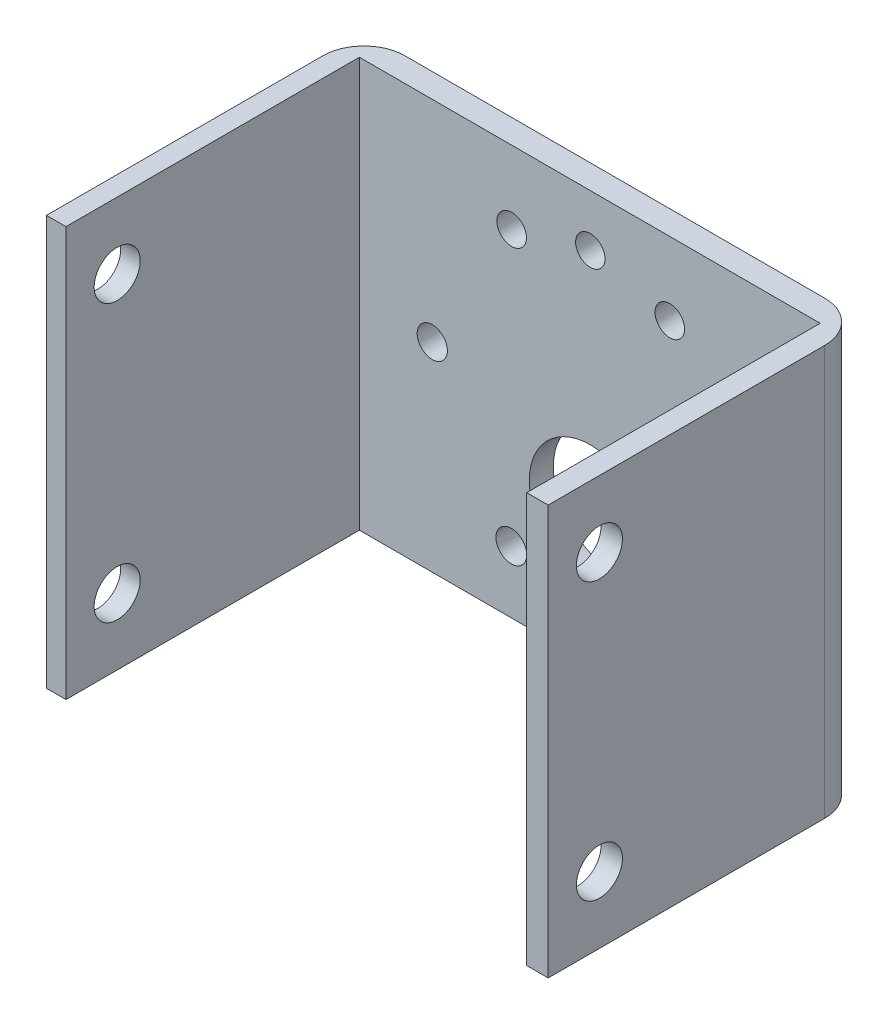
SolidWorks part; units mm, degrees
material "AISI 304"
ref_plane "Front Plane" through (0, 0, 0) normal (0, 0, 1) x (1, 0, 0)
ref_plane "Top Plane" through (0, 0, 0) normal (0, 1, 0) x (1, 0, 0)
ref_plane "Right Plane" through (0, 0, 0) normal (1, 0, 0) x (0, 0, -1)
sketch "Sketch1" plane through (0, 0, 0) normal (0, 1, 0) x (1, 0, 0)
  line L0 (-22.4033, -15.5) -> (-22.4033, 13.1532)
  line L1 (-24.5, 15.5) -> (24.5, 15.5)
  line L2 (-24.5, 15.5) -> (-24.5, -15.5)
  line L3 (-24.5, -15.5) -> (-22.4033, -15.5)
  line L4 (24.5, 15.5) -> (24.5, -15.5)
  line L7 (-22.4033, 13.1532) -> (22.2142, 13.1532)
  line L8 (22.2142, 13.1532) -> (22.2142, -15.5)
  line L10 (22.2142, -15.5) -> (24.5, -15.5)
  point P0 (0, 0)
  dimension "D1" = 31
  dimension "D2" = 49
extrude "Boss-Extrude1" add sketch "Sketch1" along normal blind 40
fillet "Fillet1" radius 4 2 edges at (24.5, 20, -15.5) (-24.5, 20, -15.5)
sketch "Sketch2" plane through (0, 0, -15.5) normal (0, 0, -1) x (-1, 0, 0)
  circle A0 centre (14, 20) radius 1.5
  circle A9 centre (-17, 20) radius 1.5
  circle A10 centre (-1.5, 4.5) radius 1.5
  circle A11 centre (-1.5, 35.5) radius 1.5
  circle A12 centre (-9.25, 6.5766) radius 1.5
  circle A13 centre (-9.25, 33.4234) radius 1.5
  circle A14 centre (6.25, 33.4234) radius 1.5
  circle A15 centre (6.25, 6.5766) radius 1.5
  circle A16 centre (-1.5, 13) radius 6
extrude "Cut-Extrude1" cut sketch "Sketch2" against normal blind 40
sketch "Sketch3" plane through (-24.5, 0, 0) normal (-1, 0, 0) x (0, 0, 1)
  line L0 (15.5, 40) -> (15.5, 0) construction
  line L1 (-11.5, 0) -> (15.5, 0) construction
  line L2 (-11.5, 40) -> (15.5, 40) construction
  circle A0 centre (10.5, 6.5) radius 2.25
  circle A1 centre (10.5, 33.5) radius 2.25
  dimension "D1" = 5
  dimension "D2" = 5
  dimension "D3" = 6.5
  dimension "D4" = 6.5
extrude "Cut-Extrude2" cut sketch "Sketch3" against normal blind 76
sketch "Sketch4" plane through (0, 0, -15.5) normal (0, 0, -1) x (-1, 0, 0)
  circle A0 centre (6.25, 33.4234) radius 1.5
  circle A1 centre (14, 20) radius 1.5
  circle A2 centre (6.25, 6.5766) radius 1.5
  circle A3 centre (-1.5, 4.5) radius 1.5
  circle A4 centre (-9.25, 6.5766) radius 1.5
  circle A5 centre (-17, 20) radius 1.5
  circle A6 centre (-1.5, 35.5) radius 1.5
  circle A7 centre (-9.25, 33.4234) radius 1.5
  circle A8 centre (-1.5, 13) radius 6
extrude "Boss-Extrude2" add sketch "Sketch4" against normal up to surface (2.3468 mm away) up to face at (-15.5, 20, -13.1532)
sketch "Sketch5" plane through (0, 0, -15.5) normal (0, 0, -1) x (-1, 0, 0)
  circle A1 centre (15.5, 20) radius 1.5
  circle A2 centre (0, 4.5) radius 1.5
  circle A3 centre (-15.5, 20) radius 1.5
  circle A4 centre (0, 35.5) radius 1.5
  circle A5 centre (7.75, 33.4234) radius 1.5
  circle A6 centre (-7.75, 33.4234) radius 1.5
  circle A7 centre (-7.75, 6.5766) radius 1.5
  circle A8 centre (7.75, 6.5766) radius 1.5
  circle A9 centre (0, 13) radius 6
extrude "Cut-Extrude3" cut sketch "Sketch5" against normal blind 10
sketch "Sketch7" plane through (0, 0, 0) normal (0, -1, 0) x (1, 0, 0)
  line L0 (-22.4033, -13.1532) -> (-22.5933, -13.1532)
  line L3 (22.2142, 15.5) -> (22.4042, 15.5)
  line L5 (22.2142, -13.1532) -> (22.4042, -13.1532)
  line L6 (22.4042, -13.1532) -> (22.4042, 15.5)
  line L7 (22.2142, -13.1532) -> (22.2142, 15.5)
  line L8 (-22.5933, -13.1532) -> (-22.5933, 15.5)
  line L9 (-24.5, 15.5) -> (-22.4033, 15.5) construction
  line L10 (-22.5933, 15.5) -> (-22.4033, 15.5)
  line L11 (-22.4033, 15.5) -> (-22.4033, -13.1532)
  dimension "D1" = 0.19
  dimension "D2" = 0.19
extrude "Cut-Extrude4" cut sketch "Sketch7" against normal blind 463
sketch "Sketch11" plane through (0, 0, -15.5) normal (0, 0, -1) x (-1, 0, 0)
  circle A0 centre (0, 13) radius 6
extrude "Boss-Extrude3" add sketch "Sketch11" against normal up to surface (2.3468 mm away) up to face at (-1.5, 35.5, -13.1532)
sketch "Sketch12" plane through (0, 0, -15.5) normal (0, 0, -1) x (-1, 0, 0)
  line L1 (-20.5, 0) -> (20.5, 0) construction
  line L2 (-20.5, 40) -> (-20.5, 0) construction
  circle A0 centre (0, 12.5) radius 6
  dimension "D1" = 12.5
  dimension "D2" = 20.5
extrude "Cut-Extrude7" cut sketch "Sketch12" against normal blind 10
sketch "Sketch13" plane through (0, 0, -15.5) normal (0, 0, -1) x (-1, 0, 0)
  circle A0 centre (7.75, 6.5766) radius 1.5
  circle A1 centre (0, 4.5) radius 1.5
  circle A2 centre (-7.75, 6.5766) radius 1.5
  circle A3 centre (-15.5, 20) radius 1.5
  circle A4 centre (-7.75, 33.4234) radius 1.5
  circle A5 centre (0, 35.5) radius 1.5
  circle A6 centre (7.75, 33.4234) radius 1.5
  circle A7 centre (15.5, 20) radius 1.5
extrude "Boss-Extrude4" add sketch "Sketch13" against normal up to surface (2.3468 mm away) up to face at (-6, 12.5, -13.1532)
sketch "Sketch14" plane through (0, 0, -15.5) normal (0, 0, -1) x (-1, 0, 0)
  circle A2 centre (15.4752, 19.4654) radius 1.4756
  circle A3 centre (-15.4752, 19.4654) radius 1.4632
  circle A4 centre (0, 3.9902) radius 1.5
  circle A5 centre (0.0421, 34.9349) radius 1.4349
  circle A6 centre (7.7526, 6.0721) radius 1.5052
  circle A7 centre (-7.7526, 6.0721) radius 1.5
  circle A8 centre (-7.7226, 32.8759) radius 1.4452
  circle A9 centre (7.7226, 32.8759) radius 1.4452
extrude "Cut-Extrude8" cut sketch "Sketch14" against normal blind 10
